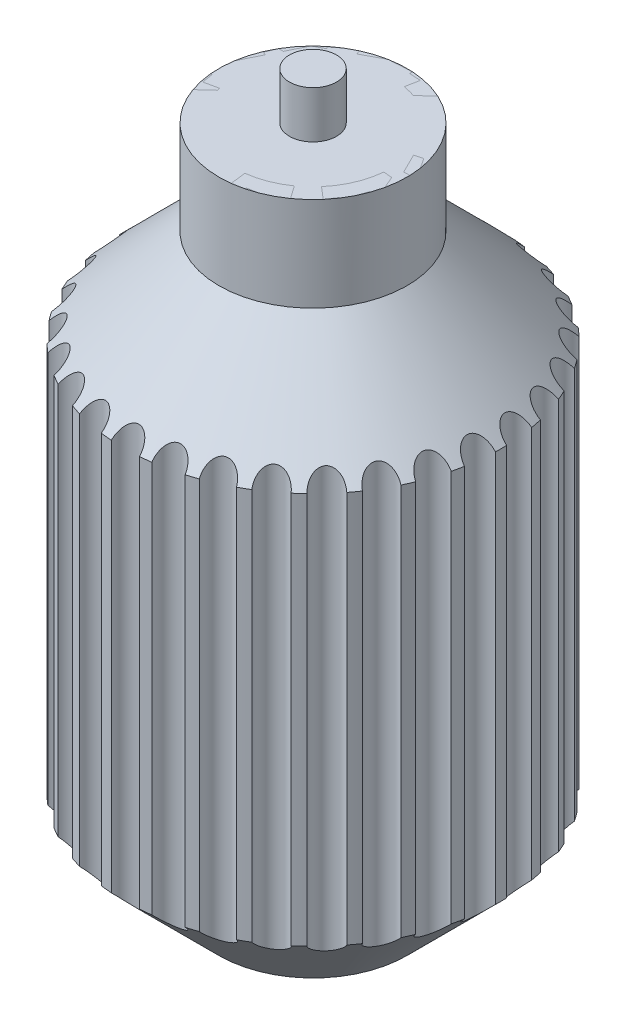
SolidWorks part; units mm, degrees
ref_plane "Front Plane" through (0, 0, 0) normal (0, 0, 1) x (1, 0, 0)
ref_plane "Top Plane" through (0, 0, 0) normal (0, 1, 0) x (1, 0, 0)
ref_plane "Right Plane" through (0, 0, 0) normal (1, 0, 0) x (0, 0, -1)
sketch "Sketch1" plane through (0, 0, 0) normal (0, 0, 1) x (1, 0, 0)
  line L0 (-30, 0) -> (-30, -30)
  line L1 (-30, -30) -> (-60, -60)
  line L2 (-60, -60) -> (-60, -185)
  line L3 (-60, -185) -> (-30, -215)
  line L4 (-30, -215) -> (0, -215)
  line L5 (-30, 0) -> (0, 0)
  line L6 (0, 0) -> (0, -215)
  line L7 (0, 0) -> (0, -388.7326) construction
  dimension "D1" = 30
  dimension "D2" = 30
  dimension "D3" = 135
  dimension "D4" = 125
  dimension "D5" = 135
  dimension "D6" = 30
  dimension "D7" = 30
revolve "Revolve1" add sketch "Sketch1" angle 360 about L7
shell "Shell1" thickness 5
ref_plane "Plane1" through (65, 0, 0) normal (1, 0, 0) x (0, 0, -1)
sketch "Sketch6" plane through (0, 0, 0) normal (0, 1, 0) x (1, 0, 0)
  circle A0 centre (0, 60) radius 4.5
  circle A1 centre (0, 0) radius 60 construction
  dimension "D1" = 9
extrude "Cut-Extrude1" cut sketch "Sketch6" against normal through all
pattern_circular "CirPattern1" count 30 over 360 about axis through (0, 0, 0) along (0, 1, 0) of "Cut-Extrude1"
surface "Surface-Fill1"
sketch "Sketch7" plane through (0, 0, 0) normal (0, 1, 0) x (1, 0, 0)
  circle A0 centre (0, 0) radius 7.5
  dimension "D1" = 15
extrude "Boss-Extrude1" add sketch "Sketch7" along normal blind 15 separate body
